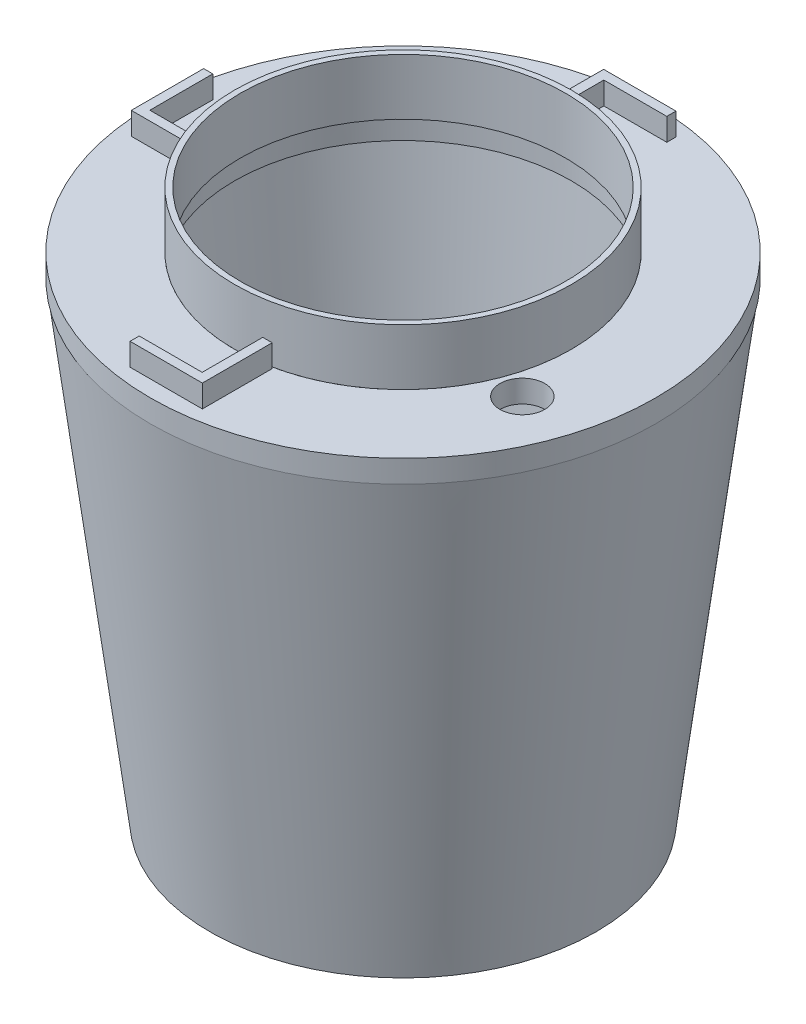
SolidWorks part; units mm, degrees
ref_plane "Front Plane" through (0, 0, 0) normal (0, 0, 1) x (1, 0, 0)
ref_plane "Top Plane" through (0, 0, 0) normal (0, 1, 0) x (1, 0, 0)
ref_plane "Right Plane" through (0, 0, 0) normal (1, 0, 0) x (0, 0, -1)
sketch "Sketch2" plane through (0, 0, 0) normal (0, 0, 1) x (1, 0, 0)
  line L8 (300, -346.365) -> (400, 453.635)
  line L9 (300, -346.365) -> (0, -346.365)
  line L10 (344.1391, -396.365) -> (0, -396.365)
  line L11 (344.1391, -396.365) -> (449.6139, 447.4332)
  line L12 (0, -346.365) -> (0, -396.365)
  line L13 (400, 453.635) -> (449.6139, 447.4332)
  line L14 (0, -396.365) -> (0, 403.635) construction
  dimension "D3" = 300
  dimension "D1" = 50
  dimension "D2" = 800
  dimension ".5" = 800
  dimension "D4" = 344.1391
  dimension "D5" = 97.125
  dimension "D6" = 262.875
  dimension "D7" = 843.7983
revolve "Revolve2" add sketch "Sketch2" angle 360 about L14
ref_plane "Plane1" through (0, 440, 0) normal (0, -1, 0) x (-1, 0, 0)
sketch "Sketch8" plane through (0, 440, 0) normal (0, -1, 0) x (-1, 0, 0)
  circle A0 centre (0, 0) radius 449.9136
  circle A1 centre (0, 0) radius 300
extrude "Boss-Extrude5" add sketch "Sketch8" against normal blind 40
sketch "Sketch9" plane through (0, 480, 0) normal (0, 1, 0) x (1, 0, 0)
  circle A0 centre (0, 0) radius 300
  circle A1 centre (0, 0) radius 290
  dimension "D1" = 580
  dimension "D2" = 600
  dimension "D3" = 600
extrude "Boss-Extrude6" add sketch "Sketch9" along normal blind 100 separate body
sketch "Sketch11" plane through (0, 440, 0) normal (0, -1, 0) x (-1, 0, 0)
  circle A0 centre (-329, -116.3908) radius 40
  circle A1 centre (0, 0) radius 300 construction
  dimension "D1" = 329
  dimension "D2" = 80
extrude "Cut-Extrude2" cut sketch "Sketch11" against normal blind 109 and the other way blind 75
sketch "Sketch12" plane through (0, 480, 0) normal (0, 1, 0) x (1, 0, 0)
  line L0 (-420.6404, 65.5609) -> (-420.6404, -63.3003)
  line L1 (-420.6404, 65.5609) -> (-404.3049, 65.5609)
  line L3 (-404.3049, -63.3003) -> (-420.6404, -63.3003)
  line L5 (-404.3049, 65.5609) -> (-404.3049, -46.5935)
  line L7 (-404.3049, -63.3003) -> (-300, -63.3003)
  line L9 (-300, -46.5935) -> (-404.3049, -46.5935)
  line L10 (-300, -46.5935) -> (-296.3597, -46.5935)
  line L11 (-296.3597, -46.5935) -> (-296.3597, -63.3003)
  line L12 (-296.3597, -63.3003) -> (-300, -63.3003)
  line L13 (65.5609, 420.6404) -> (65.5609, 404.3049)
  line L14 (65.5609, 420.6404) -> (-63.3003, 420.6404)
  line L15 (65.5609, 404.3049) -> (-46.5935, 404.3049)
  line L16 (-63.3003, 404.3049) -> (-63.3003, 300)
  line L17 (-46.5935, 300) -> (-46.5935, 404.3049)
  line L18 (-63.3003, 404.3049) -> (-63.3003, 420.6404)
  line L19 (-46.5935, 296.3597) -> (-63.3003, 296.3597)
  line L20 (-63.3003, 300) -> (-63.3003, 296.3597)
  line L21 (-46.5935, 300) -> (-46.5935, 296.3597)
  line L22 (46.5935, -300) -> (46.5935, -296.3597)
  line L23 (63.3003, -300) -> (63.3003, -296.3597)
  line L27 (-65.5609, -420.6404) -> (-65.5609, -404.3049)
  line L28 (-65.5609, -420.6404) -> (63.3003, -420.6404)
  line L29 (-65.5609, -404.3049) -> (46.5935, -404.3049)
  line L30 (63.3003, -404.3049) -> (63.3003, -300)
  line L31 (46.5935, -300) -> (46.5935, -404.3049)
  line L32 (63.3003, -404.3049) -> (63.3003, -420.6404)
  line L33 (46.5935, -296.3597) -> (63.3003, -296.3597)
  line L34 (404.3049, 63.3003) -> (420.6404, 63.3003) [skipped]
  line L35 (420.6404, -65.5609) -> (404.3049, -65.5609) [skipped]
  line L36 (420.6404, -65.5609) -> (420.6404, 63.3003) [skipped]
  line L37 (404.3049, -65.5609) -> (404.3049, 46.5935) [skipped]
  line L38 (404.3049, 63.3003) -> (300, 63.3003) [skipped]
  line L39 (300, 46.5935) -> (404.3049, 46.5935) [skipped]
  line L40 (296.3597, 46.5935) -> (296.3597, 63.3003) [skipped]
  circle A1 centre (0, 0) radius 300 construction
  dimension "D1" = 4
extrude "Boss-Extrude13" add sketch "Sketch12" along normal blind 40
